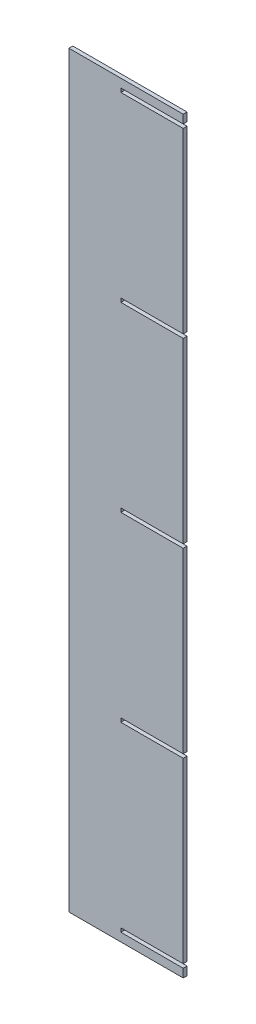
SolidWorks part; units mm, degrees
material "Oak"
ref_plane "Front Plane" through (0, 0, 0) normal (0, 0, 1) x (1, 0, 0)
ref_plane "Top Plane" through (0, 0, 0) normal (0, 1, 0) x (1, 0, 0)
ref_plane "Right Plane" through (0, 0, 0) normal (1, 0, 0) x (0, 0, -1)
sketch "Sketch1" plane through (0, 0, 0) normal (0, 0, 1) x (1, 0, 0)
  line L0 (25466.6209, 6999.9516) -> (25746.0209, 6999.9516)
  line L1 (25746.0209, 6999.9516) -> (25746.0209, 8828.7516)
  line L2 (25746.0209, 8828.7516) -> (25466.6209, 8828.7516)
  line L3 (25466.6209, 8828.7516) -> (25466.6209, 6999.9516)
  line L4 (25593.6209, 7909.6526) -> (25746.0209, 7909.6526)
  line L5 (25746.0209, 7909.6526) -> (25746.0209, 7919.0506)
  line L6 (25746.0209, 7919.0506) -> (25593.6209, 7919.0506)
  line L7 (25593.6209, 7919.0506) -> (25593.6209, 7909.6526)
  line L8 (25593.6209, 8354.1526) -> (25746.0209, 8354.1526)
  line L9 (25746.0209, 8354.1526) -> (25746.0209, 8363.5506)
  line L10 (25746.0209, 8363.5506) -> (25593.6209, 8363.5506)
  line L11 (25593.6209, 8363.5506) -> (25593.6209, 8354.1526)
  line L12 (25593.6209, 7465.1526) -> (25746.0209, 7465.1526)
  line L13 (25746.0209, 7465.1526) -> (25746.0209, 7474.5506)
  line L14 (25746.0209, 7474.5506) -> (25593.6209, 7474.5506)
  line L15 (25593.6209, 7474.5506) -> (25593.6209, 7465.1526)
  line L16 (25593.6209, 8798.6526) -> (25746.0209, 8798.6526)
  line L17 (25746.0209, 8798.6526) -> (25746.0209, 8808.0506)
  line L18 (25746.0209, 8808.0506) -> (25593.6209, 8808.0506)
  line L19 (25593.6209, 8808.0506) -> (25593.6209, 8798.6526)
  line L20 (25593.6209, 7020.6526) -> (25746.0209, 7020.6526)
  line L21 (25746.0209, 7020.6526) -> (25746.0209, 7030.0506)
  line L22 (25746.0209, 7030.0506) -> (25593.6209, 7030.0506)
  line L23 (25593.6209, 7030.0506) -> (25593.6209, 7020.6526)
extrude "Boss-Extrude1" add sketch "Sketch1" along normal blind 9.398 contours L23 L22 L1 L12 L15 L14 L4 L7 L6 L8 L11 L10 L16 L19 L18 L2 L3 L0 L20
